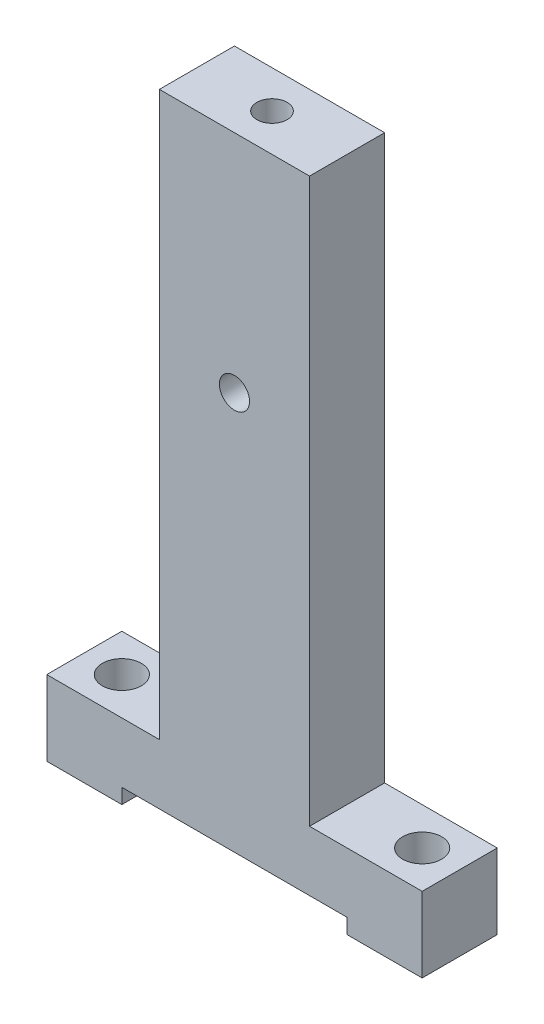
SolidWorks part; units mm, degrees
ref_plane "Front Plane" through (0, 0, 0) normal (0, 0, 1) x (1, 0, 0)
ref_plane "Top Plane" through (0, 0, 0) normal (0, 1, 0) x (1, 0, 0)
ref_plane "Right Plane" through (0, 0, 0) normal (1, 0, 0) x (0, 0, -1)
sketch "Sketch1" plane through (0, 0, 0) normal (0, 1, 0) x (1, 0, 0)
  line L1 (-31.75, 6.35) -> (31.75, 6.35)
  line L2 (-31.75, 6.35) -> (-31.75, -6.35)
  line L3 (-31.75, -6.35) -> (31.75, -6.35)
  line L4 (31.75, 6.35) -> (31.75, -6.35)
  dimension "D1" = 6.35
  dimension "D2" = 6.35
  dimension "D3" = 31.75
  dimension "D4" = 31.75
extrude "Boss-Extrude1" add sketch "Sketch1" along normal mid plane 107.95
sketch "Sketch2" plane through (0, 0, 6.35) normal (0, 0, 1) x (1, 0, 0)
  line L0 (-31.75, -53.975) -> (31.75, -53.975) construction
  line L1 (-31.75, 53.975) -> (-12.7, 53.975)
  line L2 (-31.75, 53.975) -> (-31.75, -41.275)
  line L3 (-31.75, -41.275) -> (-12.7, -41.275)
  line L4 (-12.7, 53.975) -> (-12.7, -41.275)
  line L5 (31.75, 53.975) -> (12.7, 53.975)
  line L6 (31.75, 53.975) -> (31.75, -41.275)
  line L7 (31.75, -41.275) -> (12.7, -41.275)
  line L8 (12.7, 53.975) -> (12.7, -41.275)
  dimension "D1" = 12.7
  dimension "D2" = 12.7
  dimension "D3" = 12.7
  dimension "D4" = 12.7
extrude "Cut-Extrude1" cut sketch "Sketch2" against normal up to next
sketch "Sketch3" plane through (0, -41.275, 0) normal (0, 1, 0) x (1, 0, 0)
  circle A0 centre (-25.4, 0) radius 3.302
  circle A1 centre (25.4, 0) radius 3.302
  dimension "D1" = 50.8
  dimension "D2" = 25.4
extrude "Cut-Extrude2" cut sketch "Sketch3" against normal through all
hole_wizard "1/4-20 Tapped Hole1" positions "Sketch5" profile "Sketch4" tap size "1/4-20" standard "ANSI Inch"
sketch "Sketch5" plane through (0, 53.975, 0) normal (0, 1, 0) x (1, 0, 0)
  point P0 (0, 0)
sketch "Sketch4" plane through (0, 53.975, 0) normal (1, 0, 0) x (0, 0, 1)
  line L0 (0, 0) -> (0, 20.5838)
  line L1 (0, 20.5838) -> (2.5527, 19.05)
  line L2 (2.5527, 19.05) -> (2.5527, 0)
  line L5 (2.5527, 0) -> (0, 0)
  line L10 (0, 20.5838) -> (-2.5527, 19.05) construction
  line L11 (0, -6.35) -> (0, 107.95) construction
  dimension "Tap Drill Dia." = 5.1054
  dimension "Tap Drill Depth" = 19.05
  dimension "Drill Angle" = 118
cosmetic thread "Hole Thread1" parameters "D1"=12.7, "D2"=6.35
sketch "Sketch6" plane through (0, 0, 6.35) normal (0, 0, 1) x (1, 0, 0)
  line L0 (-31.75, -53.975) -> (31.75, -53.975) construction
  line L1 (-19.05, -53.975) -> (19.05, -53.975)
  line L2 (-19.05, -53.975) -> (-19.05, -51.435)
  line L3 (-19.05, -51.435) -> (19.05, -51.435)
  line L4 (19.05, -53.975) -> (19.05, -51.435)
  line L5 (31.75, -41.275) -> (31.75, -53.975) construction
  line L6 (-31.75, -41.275) -> (-31.75, -53.975) construction
  dimension "D1" = 2.54
  dimension "D2" = 12.7
  dimension "D3" = 12.7
extrude "Cut-Extrude3" cut sketch "Sketch6" against normal through all
hole_wizard "1/4-20 Tapped Hole2" positions "Sketch8" profile "Sketch7" tap size "1/4-20" standard "ANSI Inch"
sketch "Sketch8" plane through (0, 0, 6.35) normal (0, 0, 1) x (1, 0, 0)
  line L0 (-12.7, 53.975) -> (12.7, 53.975) construction
  point P0 (0, 15.875)
  dimension "D1" = 38.1
sketch "Sketch7" plane through (0, 15.875, 6.35) normal (1, 0, 0) x (0, -1, 0)
  line L0 (0, 0) -> (0, 26.9338)
  line L1 (0, 26.9338) -> (2.5527, 25.4)
  line L2 (2.5527, 25.4) -> (2.5527, 0)
  line L5 (2.5527, 0) -> (0, 0)
  line L10 (0, 26.9338) -> (-2.5527, 25.4) construction
  line L11 (0, -6.35) -> (0, 107.95) construction
  dimension "Tap Drill Dia." = 5.1054
  dimension "Tap Drill Depth" = 25.4
  dimension "Drill Angle" = 118
cosmetic thread "Hole Thread2" parameters "D1"=12.7, "D2"=6.35
